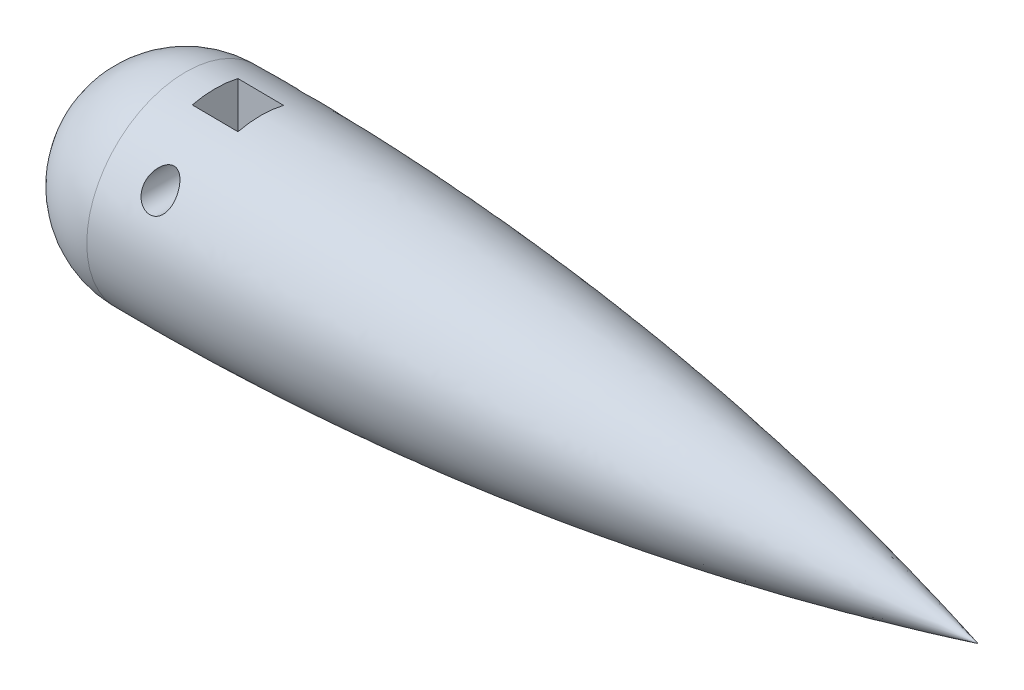
SolidWorks part; units mm, degrees
material "Pure Lead"
ref_plane "Front Plane" through (0, 0, 0) normal (0, 0, 1) x (1, 0, 0)
ref_plane "Top Plane" through (0, 0, 0) normal (0, 1, 0) x (1, 0, 0)
ref_plane "Right Plane" through (0, 0, 0) normal (1, 0, 0) x (0, 0, -1)
curve "Curve1"
  spline degree 3 poles (25.4, 0.032, 0) (24.9768, 0.0904, 0) (24.1307, 0.2071, 0) (22.8605, 0.3691, 0) (21.5905, 0.5229, 0) (20.3205, 0.6676, 0) (19.0504, 0.804, 0) (17.7804, 0.9321, 0) (16.5104, 1.0514, 0) (15.2404, 1.1606, 0) (13.9704, 1.2598, 0) (12.692, 1.3473, 0) (11.4135, 1.4221, 0) (10.1349, 1.4776, 0) (8.8649, 1.5185, 0) (7.8146, 1.5178, 0) (6.9766, 1.5373, 0) (6.35, 1.546, 0) (5.715, 1.5506, 0) (5.0799, 1.5478, 0) (4.4448, 1.5346, 0) (3.8095, 1.5078, 0) (3.1738, 1.462, 0) (2.5803, 1.3959, 0) (2.0289, 1.3055, 0) (1.6052, 1.2091, 0) (1.2675, 1.107, 0) (1.012, 1.0136, 0) (0.7549, 0.8965, 0) (0.4933, 0.743, 0) (0.2762, 0.5635, 0) (0.0851, 0.3233, 0) (-0.0556, 0, 0) (0.0851, -0.3233, 0) (0.2762, -0.5635, 0) (0.4933, -0.743, 0) (0.7549, -0.8965, 0) (1.012, -1.0136, 0) (1.2675, -1.107, 0) (1.6052, -1.2091, 0) (2.0289, -1.3055, 0) (2.5803, -1.3959, 0) (3.1738, -1.462, 0) (3.8095, -1.5078, 0) (4.4448, -1.5346, 0) (5.0799, -1.5478, 0) (5.715, -1.5506, 0) (6.35, -1.546, 0) (6.9766, -1.5373, 0) (7.8146, -1.5178, 0) (8.8649, -1.5185, 0) (10.1349, -1.4776, 0) (11.4135, -1.4221, 0) (12.692, -1.3473, 0) (13.9704, -1.2598, 0) (15.2404, -1.1606, 0) (16.5104, -1.0514, 0) (17.7804, -0.9321, 0) (19.0504, -0.804, 0) (20.3205, -0.6676, 0) (21.5905, -0.5229, 0) (22.8605, -0.3691, 0) (24.1307, -0.2071, 0) (24.9768, -0.0904, 0) (25.4, -0.032, 0) knots 0 0 0 0 0.024634 0.049243 0.07383 0.098397 0.122946 0.147479 0.171995 0.196494 0.220976 0.245442 0.27038 0.294813 0.319232 0.343642 0.35536 0.367566 0.379771 0.391975 0.404183 0.416399 0.428636 0.44092 0.450818 0.460843 0.465946 0.471149 0.476523 0.482208 0.488618 0.492568 0.5 0.507432 0.511382 0.517792 0.523477 0.528851 0.534054 0.539157 0.549182 0.55908 0.571364 0.583601 0.595817 0.608025 0.620229 0.632434 0.64464 0.656358 0.680768 0.705187 0.72962 0.754558 0.779024 0.803506 0.828005 0.852521 0.877054 0.901603 0.92617 0.950757 0.975366 1 1 1 1
sketch "Sketch1" plane through (0, 0, 0) normal (0, 0, 1) x (1, 0, 0)
  line L2 (0, 0) -> (28.575, 0)
  line L3 (3.175, 0) -> (3.175, -3.175) construction
  arc A0 (0, 0) -> (3.175, -3.175) centre (3.175, 0) ccw
  arc A1 (3.175, -3.175) -> (28.575, 0) centre (4.0089, 93.3414) ccw
  dimension "D1" = 3.175
  dimension "D3" = 96.52
  dimension "D2" = 28.575
revolve "Revolve1" add sketch "Sketch1" angle 360 about L2
scale "Scale1" scale about origin uniform scaling yes scale factor 13.1
ref_plane "Plane1" through (0, 41.91, 0) normal (0, 1, 0) x (1, 0, 0)
sketch "Sketch2" plane through (0, 41.91, 0) normal (0, 1, 0) x (1, 0, 0)
  line L0 (25.4, 0) -> (0, 0) construction
  line L1 (53.9115, -9.5885) -> (73.0885, -9.5885)
  line L2 (53.9115, -9.5885) -> (53.9115, 9.5885)
  line L3 (53.9115, 9.5885) -> (73.0885, 9.5885)
  line L4 (73.0885, -9.5885) -> (73.0885, 9.5885)
  line L5 (53.9115, -9.5885) -> (73.0885, 9.5885) construction
  line L6 (53.9115, 9.5885) -> (73.0885, -9.5885) construction
  point P0 (63.5, 0)
  dimension "D1" = 19.177
  dimension "D2" = 19.177
  dimension "D3" = 63.5
extrude "Cut-Extrude1" cut sketch "Sketch2" against normal blind 38.1
ref_plane "Plane3" through (0, 0, 38.1) normal (0, 0, -1) x (-1, 0, 0)
sketch "Sketch8" plane through (0, 0, 38.1) normal (0, 0, -1) x (-1, 0, 0)
  circle A0 centre (-63.5, 25.4) radius 2.667
  dimension "D3" = 5.334
  dimension "D1" = 63.5
  dimension "D2" = 25.4
extrude "Cut-Extrude3" cut sketch "Sketch8" along normal through all
sketch "Sketch9" plane through (0, 0, 38.1) normal (0, 0, -1) x (-1, 0, 0)
  circle A0 centre (-63.5, 25.4) radius 6.35
  dimension "D1" = 12.7
extrude "Cut-Extrude4" cut sketch "Sketch9" along normal blind 19.05
mirror "Mirror1" about plane through (0, 0, 0) normal (0, 0, 1) of "Cut-Extrude4"
